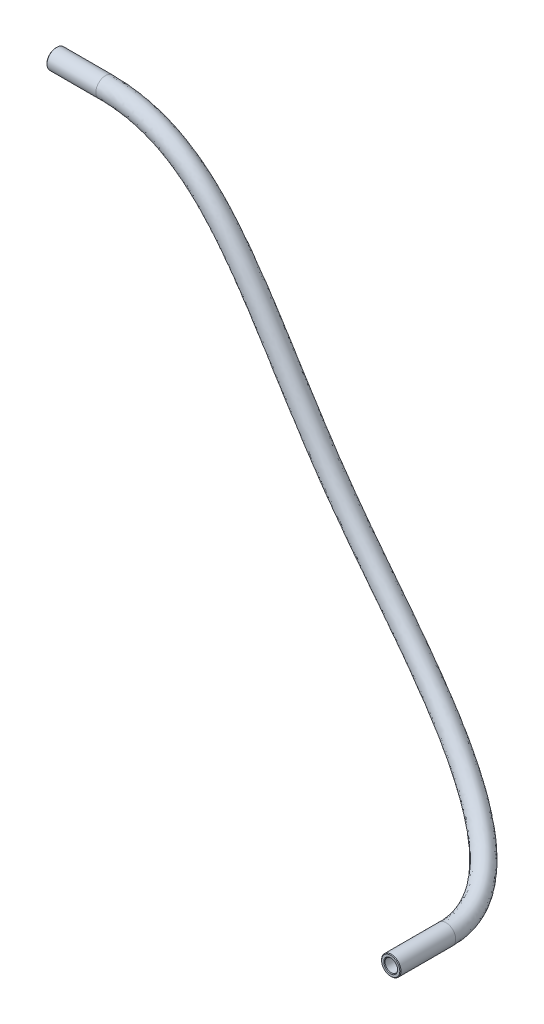
SolidWorks part; units mm, degrees
ref_plane "Front Plane" through (0, 0, 0) normal (0, 0, 1) x (1, 0, 0)
ref_plane "Top Plane" through (0, 0, 0) normal (0, 1, 0) x (1, 0, 0)
ref_plane "Right Plane" through (0, 0, 0) normal (1, 0, 0) x (0, 0, -1)
sketch3d "3DSketch1"
  line L0 (201.3105, -198.3536, 61.0875) -> (201.3105, -198.3536, 49.6875)
  line L1 (96.825, -106.4823, 25.525) -> (107.025, -106.4823, 25.525)
  spline S0 degree 3 poles (201.3105, -198.3536, 49.6875) (201.3105, -198.3536, 29.1968) (143.6274, -152.4179, 24.8569) (130.5586, -106.4823, 25.525) (107.025, -106.4823, 25.525) knots 0 0 0 0 0.472509 1 1 1 1
sketch "Sketch3" plane through (104.925, 0, 0) normal (1, 0, 0) x (0, 0, -1)
  circle A0 centre (-25.525, -106.4823) radius 1.3
  circle A1 centre (-25.525, -106.4823) radius 2
  circle A2 centre (-25.525, -106.4823) radius 3.5 construction
  dimension "D1" = 2.6
  dimension "D2" = 4
sweep "Sweep1" add profiles "Sketch3" path "3DSketch1"
chamfer "Chamfer1" distance 0.127 angle 45 4 edges at (96.825, -104.4823, 25.525) (96.825, -105.1823, 25.525) (202.305, -196.6183, 61.0875) (201.9569, -197.2257, 61.0875)
